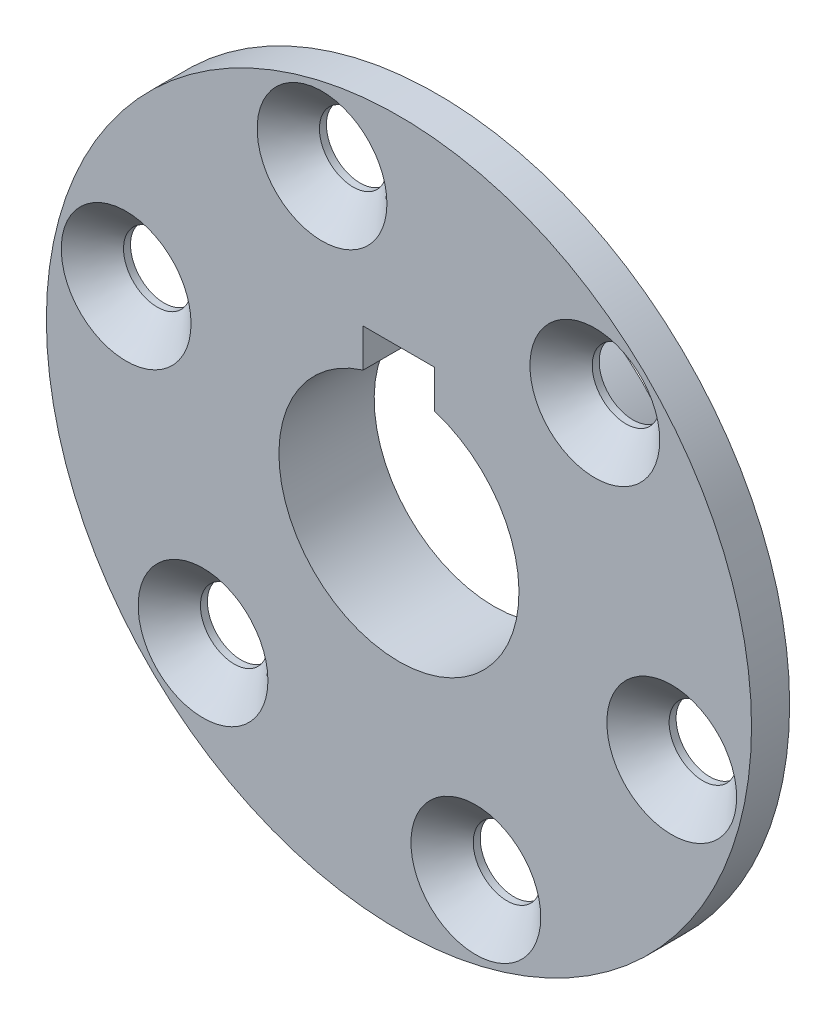
SolidWorks part; units mm, degrees
material "AISI 1045 Steel, cold drawn"
ref_plane "Front Plane" through (0, 0, 0) normal (0, 0, 1) x (1, 0, 0)
ref_plane "Top Plane" through (0, 0, 0) normal (0, 1, 0) x (1, 0, 0)
ref_plane "Right Plane" through (0, 0, 0) normal (1, 0, 0) x (0, 0, -1)
sketch "Sketch1" plane through (0, 0, 0) normal (0, 0, 1) x (1, 0, 0)
  line L0 (0, 0) -> (0, 16) construction
  line L2 (-4.7625, 20.3548) -> (-4.7625, 15.2748)
  line L3 (4.7625, 20.3548) -> (4.7625, 15.2748)
  line L4 (-4.7625, 20.3548) -> (4.7625, 20.3548)
  circle A0 centre (0, 0) radius 47
  arc A2 (4.7625, 15.2748) -> (-4.7625, 15.2748) centre (0, 0) cw
  circle A3 centre (0, 0) radius 16 construction
  dimension "D1" = 94
  dimension "D2" = 9.525
  dimension "D3" = 5.08
extrude "Boss-Extrude1" add sketch "Sketch1" along normal blind 5.08
sketch "Sketch9" plane through (0, 0, 5.08) normal (0, 0, 1) x (1, 0, 0)
  circle A0 centre (-10.2515, 36.0716) radius 4
  circle A1 centre (26.1131, 26.9138) radius 4
  circle A2 centre (36.3646, -9.1577) radius 4
  circle A3 centre (10.2515, -36.0716) radius 4
  circle A4 centre (-26.1131, -26.9138) radius 4
  circle A5 centre (-36.3646, 9.1577) radius 4
  point P16 (0, 0)
  dimension "D2" = 8
  dimension "D1" = 37.5
  dimension "D3" = 6
hole_wizard "CSK for M8 Flat Head Machine Screw1" positions "3DSketch1" profile "Sketch10" countersink size "M8" standard "ANSI Metric" end condition through all
sketch3d "3DSketch1"
  point P0 (-10.2515, 36.0716, 5.08)
  point P3 (26.1131, 26.9138, 5.08)
  point P6 (-36.3646, 9.1577, 5.08)
  point P9 (36.3646, -9.1577, 5.08)
  point P12 (10.2515, -36.0716, 5.08)
  point P15 (-26.1131, -26.9138, 5.08)
sketch "Sketch10" plane through (-10.2515, 36.0716, 5.08) normal (1, 0, 0) x (0, -1, 0)
  line L0 (0, 0) -> (0, 5.08)
  line L1 (0, 5.08) -> (4.5, 5.08)
  line L2 (4.5, 5.08) -> (4.5, 4.15)
  line L3 (4.5, 4.15) -> (8.65, 0)
  line L5 (8.65, 0) -> (0, 0)
  line L6 (-4.5, 4.15) -> (-8.65, 0) construction
  line L11 (0, -6.35) -> (0, 107.95) construction
  dimension "Thru Hole Dia." = 9
  dimension "Thru Hole Depth" = 5.08
  dimension "Near C'Sink Dia." = 17.3
  dimension "Near C'Sink Angle" = 90
sketch "Sketch11" plane through (0, 0, 0) normal (0, 0, -1) x (-1, 0, 0)
  line L0 (-4.7625, 20.3548) -> (4.7625, 20.3548)
  line L1 (4.7625, 20.3548) -> (4.7625, 15.2748)
  line L2 (4.7625, 15.2748) -> (4.7625, 20.3548)
  line L3 (-4.7625, 20.3548) -> (-4.7625, 15.2748)
  line L4 (-4.7625, 15.2748) -> (-4.7625, 20.3548)
  circle A0 centre (0, 0) radius 27.94
  arc A1 (4.7625, 15.2748) -> (-5, 15.1987) centre (0, 0) cw
  arc A2 (-4.7625, 15.2748) -> (4.7625, 15.2748) centre (0, 0) ccw construction
  line M28 (-4.7625, 15.2748) -> (-4.7625, 20.3548)
  line M29 (-4.7625, 20.3548) -> (4.7625, 20.3548)
  line M30 (4.7625, 20.3548) -> (4.7625, 15.2748)
  arc M31 (4.7625, 15.2748) -> (-4.7625, 15.2748) centre (0, 0) cw
  dimension "D1" = 55.88
extrude "Boss-Extrude2" add sketch "Sketch11" along normal blind 7.62 contours A0 M31 M28 M29 M30
